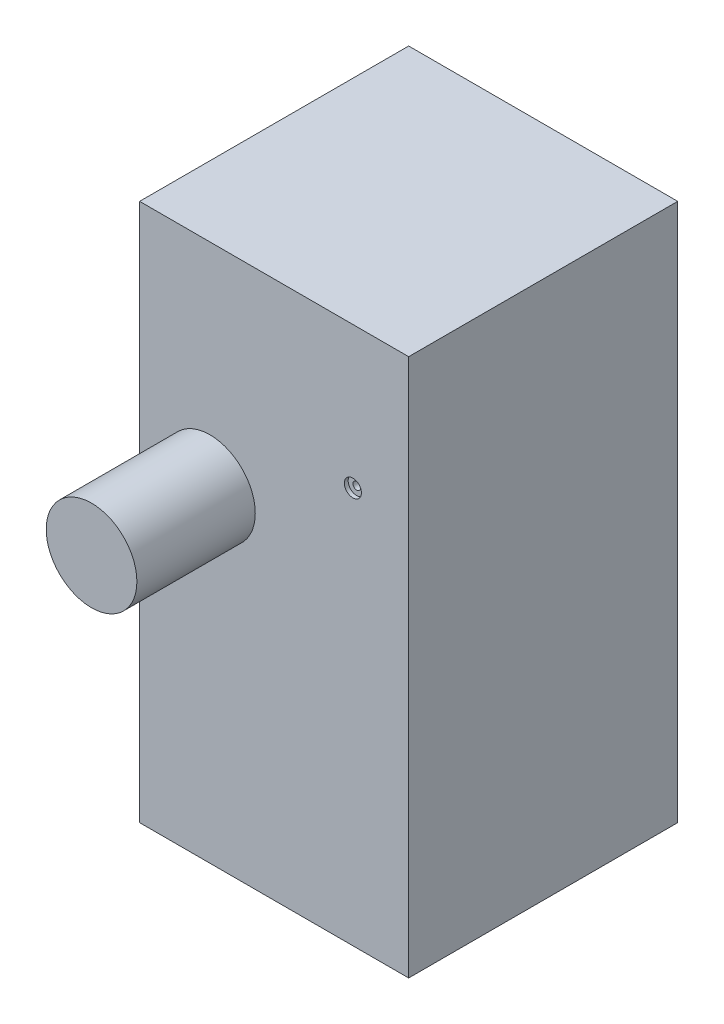
SolidWorks part; units mm, degrees
material "1023 Carbon Steel Sheet (SS)"
ref_plane "Front Plane" through (0, 0, 0) normal (0, 0, 1) x (1, 0, 0)
ref_plane "Top Plane" through (0, 0, 0) normal (0, 1, 0) x (1, 0, 0)
ref_plane "Right Plane" through (0, 0, 0) normal (1, 0, 0) x (0, 0, -1)
sketch "Sketch1" plane through (0, 0, 0) normal (0, 1, 0) x (1, 0, 0)
  line L1 (0, 0) -> (-50, 0)
  line L2 (0, 0) -> (0, 50)
  line L3 (0, 50) -> (-50, 50)
  line L4 (-50, 0) -> (-50, 50)
extrude "Boss-Extrude1" add sketch "Sketch1" along normal blind 100 contours L2 L1 L4 L3
sketch3d "3DSketch1" plane through (0, 0, 0) normal (0, 0, 1) x (1, 0, 0)
sketch "Sketch2" plane through (0, 0, 0) normal (0, 0, 1) x (1, 0, 0)
  circle A0 centre (-36.9369, 60.5397) radius 8.4272
  circle A1 centre (-36.9369, 60.5397) radius 10.9713
extrude "Boss-Extrude2" add sketch "Sketch2" along normal blind 22 contours A0
hole_wizard "CBORE for #00 Binding Head Machine Screw1" positions "Sketch4" profile "Sketch3" counterbore size "#00" standard "ANSI Inch" end condition through all
sketch "Sketch4" plane through (0, 0, 0) normal (0, 0, 1) x (1, 0, 0)
  point P0 (-10.3679, 73.6789)
sketch "Sketch3" plane through (-10.3679, 73.6789, 0) normal (1, 0, 0) x (0, -1, 0)
  line L0 (0, 0) -> (0, 50)
  line L1 (0, 50) -> (0.6985, 50)
  line L3 (0.6985, 50) -> (0.6985, 0.7112)
  line L4 (0.6985, 0.7112) -> (1.5875, 0.7112)
  line L5 (1.5875, 0.7112) -> (1.5875, 0)
  line L7 (1.5875, 0) -> (0, 0)
  line L11 (0, -6.35) -> (0, 107.95) construction
  dimension "Thru Hole Dia." = 1.397
  dimension "Thru Hole Depth" = 50
  dimension "C'Bore Dia." = 3.175
  dimension "C'Bore Depth" = 0.7112
